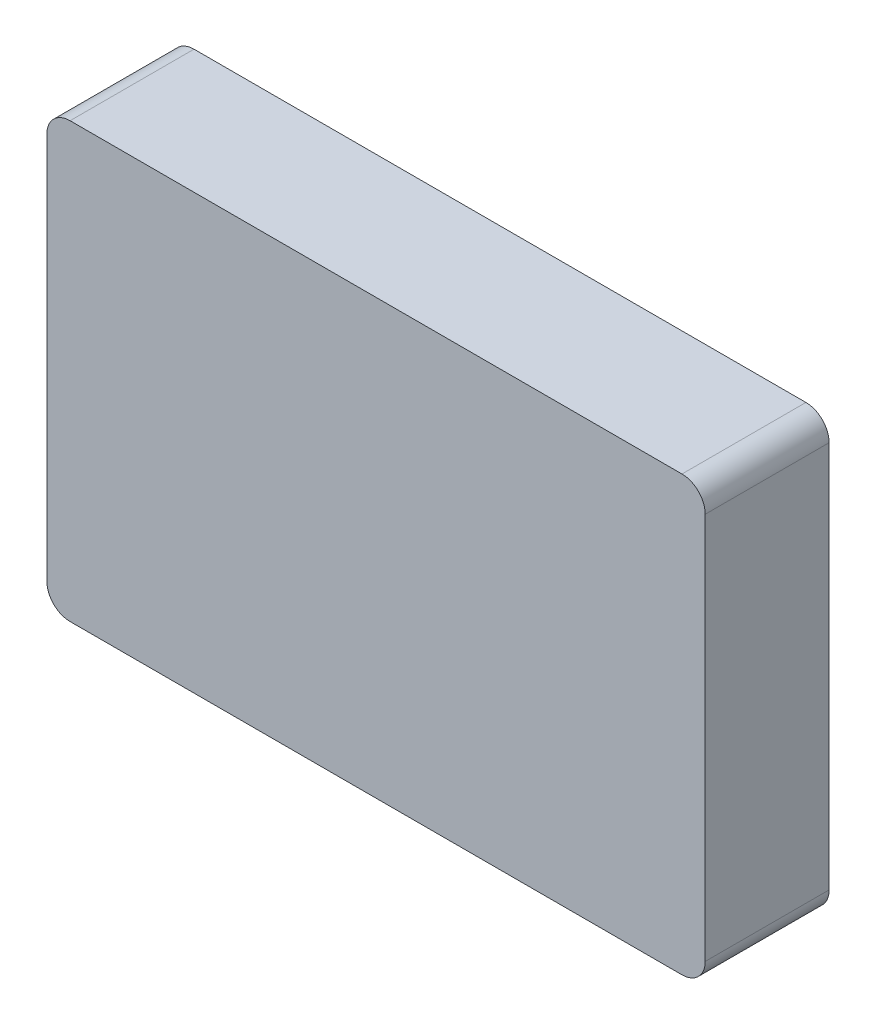
SolidWorks part; units mm, degrees
ref_plane "Front Plane" through (0, 0, 0) normal (0, 0, 1) x (1, 0, 0)
ref_plane "Top Plane" through (0, 0, 0) normal (0, 1, 0) x (1, 0, 0)
ref_plane "Right Plane" through (0, 0, 0) normal (1, 0, 0) x (0, 0, -1)
sketch "Sketch1" plane through (0, 0, 0) normal (0, 0, 1) x (1, 0, 0)
  line L0 (0, 28) -> (0, -28) construction
  line L1 (-39.5, 28) -> (39.5, 28)
  line L2 (-42.5, 25) -> (-42.5, -25)
  line L3 (-39.5, -28) -> (39.5, -28)
  line L4 (42.5, 25) -> (42.5, -25)
  line L5 (-42.5, 0) -> (42.5, 0) construction
  arc A0 (39.5, 28) -> (42.5, 25) centre (39.5, 25) cw
  arc A1 (39.5, -28) -> (42.5, -25) centre (39.5, -25) ccw
  arc A2 (-39.5, -28) -> (-42.5, -25) centre (-39.5, -25) cw
  arc A3 (-42.5, 25) -> (-39.5, 28) centre (-39.5, 25) cw
  point P6 (42.5, 28)
  point P9 (42.5, -28)
  point P14 (-42.5, 28)
  point P19 (0, 0)
  dimension "D2" = 3
  dimension "D1" = 56
  dimension "85" = 85
  dimension "D3" = 0
extrude "Boss-Extrude1" add sketch "Sketch1" along normal blind 16
